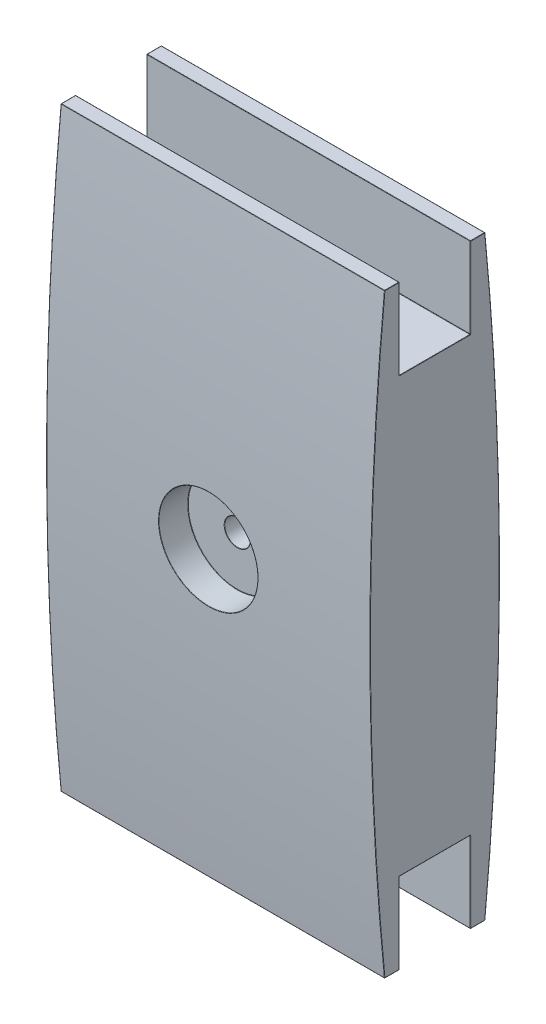
SolidWorks part; units mm, degrees
ref_plane "Front Plane" through (0, 0, 0) normal (0, 0, 1) x (1, 0, 0)
ref_plane "Top Plane" through (0, 0, 0) normal (0, 1, 0) x (1, 0, 0)
ref_plane "Right Plane" through (0, 0, 0) normal (1, 0, 0) x (0, 0, -1)
sketch "Sketch2" plane through (0, 0, 0) normal (1, 0, 0) x (0, 0, -1)
  line L0 (0, 92) -> (0, -92) construction
  line L1 (-20, -92) -> (20, -92) construction
  line L2 (-20, -92) -> (-20, 92) construction
  line L3 (-20, 92) -> (20, 92) construction
  line L4 (20, -92) -> (20, 92) construction
  line L5 (-20, -92) -> (20, 92) construction
  line L6 (-20, 92) -> (20, -92) construction
  line L7 (-20, 0) -> (20, 0) construction
  line L8 (-11, 92) -> (11, 92) construction
  line L9 (-11, 92) -> (-11, 67)
  line L10 (-11, 67) -> (11, 67)
  line L11 (11, 92) -> (11, 67)
  line L12 (-11, 92) -> (11, 67) construction
  line L13 (-11, 67) -> (11, 92) construction
  line L14 (-11, -92) -> (-11, -67)
  line L15 (11, -92) -> (11, -67)
  line L16 (-11, -67) -> (11, -67)
  line L17 (-20, 92) -> (-11, 92) construction
  line L18 (11, 92) -> (20, 92) construction
  line L19 (-20, -92) -> (-11, -92) construction
  line L20 (11, -92) -> (20, -92) construction
  line L21 (-15.5, 92) -> (-11, 92)
  line L22 (11, 92) -> (15.5, 92)
  line L23 (-15.5, -92) -> (-11, -92)
  line L24 (11, -92) -> (15.5, -92)
  arc A0 (-15.5, 92) -> (-15.5, -92) centre (922.6944, 0) ccw
  arc A1 (15.5, 92) -> (15.5, -92) centre (-922.6944, 0) cw
  point P0 (0, 0)
  point P8 (0, 79.5)
  point P19 (-15.5, 92)
  point P20 (-15.5, -92)
  dimension "D1" = 40
  dimension "D2" = 134
  dimension "D3" = 22
  dimension "D4" = 25
extrude "Boss-Extrude1" add sketch "Sketch2" along normal blind 100
ref_plane "Plane1" through (0, 0, 20) normal (0, 0, 1) x (1, 0, 0)
sketch "Sketch4" plane through (0, 0, 20) normal (0, 0, 1) x (1, 0, 0)
  line L0 (50, 92) -> (50, -92) construction
  line L4 (0, 92) -> (0, -92)
  line L5 (0, -92) -> (100, -92)
  line L6 (100, -92) -> (100, 92)
  line L7 (100, 92) -> (0, 92)
  line L8 (0, 92) -> (0, -92)
  line L9 (0, -92) -> (100, -92)
  line L10 (100, -92) -> (100, 92)
  line L11 (100, 92) -> (0, 92)
  circle A0 centre (50, 0) radius 15.2786
  dimension "D1" = 0
extrude "Cut-Extrude1" cut sketch "Sketch4" against normal blind 9 contours A0
mirror "Mirror1" about plane through (0, 0, 0) normal (0, 0, 1) of "Cut-Extrude1"
sketch "Sketch5" plane through (0, 0, 20) normal (0, 0, 1) x (1, 0, 0)
  circle A0 centre (50, 0) radius 4
  dimension "D1" = 8
extrude "Cut-Extrude2" cut sketch "Sketch5" against normal through all both and the other way through all
fillet "Fillet1" radius 0.1 42 edges at (50, 92, 11) (50, 92, -11) (50, 67, -11) (50, 67, 11) (54, 0, 11) (65.2786, 0, 11) (50, -92, 11) (50, -92, -11) (50, -67, 11) (50, -67, -11) (100, 92, -13.25) (100, -92, -13.25) (100, -79.5, -11) (100, -67, 0) (100, -79.5, 11) (100, -92, 13.25) (100, 92, 13.25) (100, 79.5, 11) (100, 67, 0) (100, 79.5, -11) (50, 92, 15.5) (100, 0, 20) (50, -92, 15.5) (35.1305, 3.5121, 19.9935) (65.2786, 0, -11) (46, 0, -11) (64.8695, -3.5121, -19.9935) (50, -92, -15.5) (100, 0, -20) (50, 92, -15.5) (0, 67, 0) (0, 79.5, 11) (0, 92, 13.25) (0, 0, 20) (0, -92, 13.25) (0, -79.5, 11) (0, -67, 0) (0, -79.5, -11) (0, -92, -13.25) (0, 0, -20) (0, 92, -13.25) (0, 79.5, -11)
